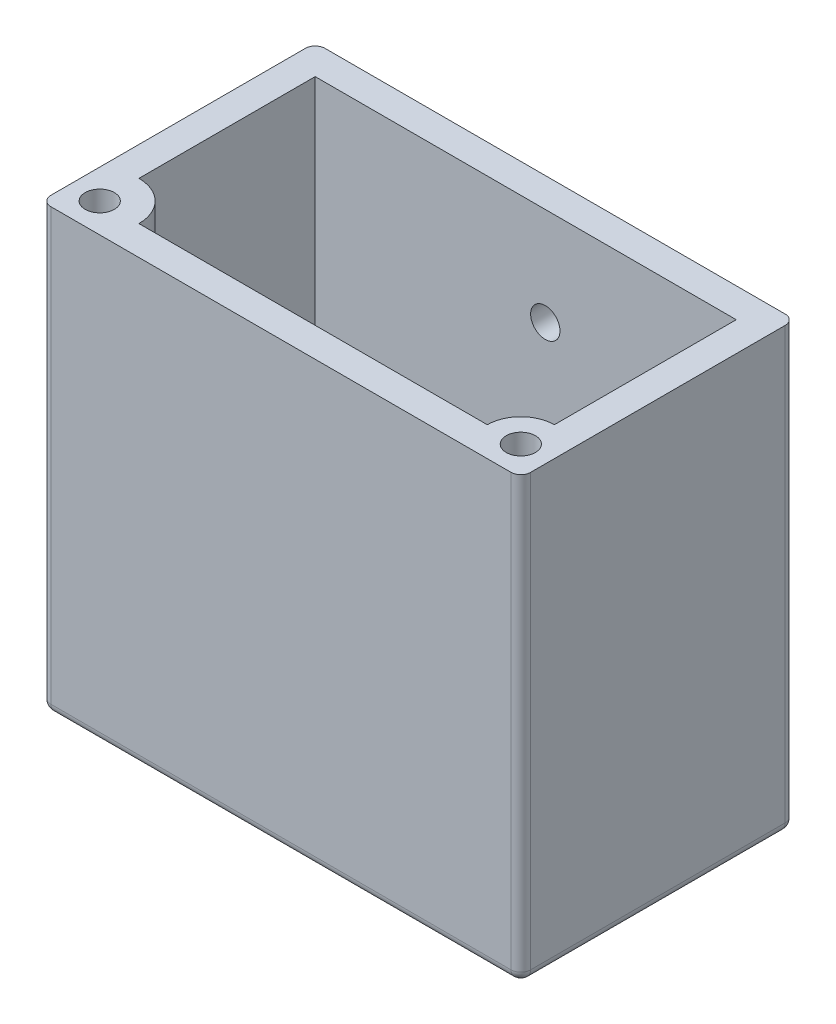
SolidWorks part; units mm, degrees
ref_plane "Front Plane" through (0, 0, 0) normal (0, 0, 1) x (1, 0, 0)
ref_plane "Top Plane" through (0, 0, 0) normal (0, 1, 0) x (1, 0, 0)
ref_plane "Right Plane" through (0, 0, 0) normal (1, 0, 0) x (0, 0, -1)
sketch "Sketch1" plane through (0, 0, 0) normal (0, 1, 0) x (1, 0, 0)
  line L1 (-29.4867, 17.2212) -> (19.5133, 17.2212)
  line L2 (-29.4867, 17.2212) -> (-29.4867, -10.7788)
  line L3 (-29.4867, -10.7788) -> (19.5133, -10.7788)
  line L4 (19.5133, 17.2212) -> (19.5133, -10.7788)
  dimension "D1" = 28
  dimension "D2" = 49
extrude "Boss-Extrude1" add sketch "Sketch1" along normal blind 45
sketch "Sketch2" plane through (0, 45, 0) normal (0, 1, 0) x (1, 0, 0)
  line L0 (-29.4867, -10.7788) -> (19.5133, -10.7788) construction
  line L1 (16.5133, -7.7788) -> (-26.4867, -7.7788)
  line L2 (16.5133, -7.7788) -> (16.5133, 14.2212)
  line L3 (16.5133, 14.2212) -> (-26.4867, 14.2212)
  line L4 (-26.4867, -7.7788) -> (-26.4867, 14.2212)
  line L5 (-29.4867, 17.2212) -> (-29.4867, -10.7788) construction
  line L6 (19.5133, 17.2212) -> (-29.4867, 17.2212) construction
  line L7 (19.5133, -10.7788) -> (19.5133, 17.2212) construction
  dimension "D1" = 3
  dimension "D2" = 3
  dimension "D3" = 3
  dimension "D4" = 3
extrude "Cut-Extrude1" cut sketch "Sketch2" against normal blind 43
sketch "Sketch3" plane through (0, 2, 0) normal (0, 1, 0) x (1, 0, 0)
  line L0 (16.5133, 14.2212) -> (-26.4867, 14.2212) construction
  line L1 (9.5133, 3.2212) -> (-19.4867, 3.2212)
  line L2 (9.5133, 3.2212) -> (9.5133, 11.2212)
  line L3 (9.5133, 11.2212) -> (-19.4867, 11.2212)
  line L4 (-19.4867, 3.2212) -> (-19.4867, 11.2212)
  line L5 (16.5133, -7.7788) -> (16.5133, 14.2212) construction
  line L6 (-26.4867, 14.2212) -> (-26.4867, -7.7788) construction
  dimension "D1" = 8
  dimension "D2" = 3
  dimension "D3" = 7
  dimension "D4" = 7
extrude "Cut-Extrude2" cut sketch "Sketch3" against normal blind 3
sketch "Sketch4" plane through (0, 0, -14.2212) normal (0, 0, 1) x (1, 0, 0)
  line L0 (16.5133, 2) -> (-26.4867, 2) construction
  line L1 (16.5133, 2) -> (16.5133, 45) construction
  circle A0 centre (-2.9867, 35) radius 1.5
  dimension "D1" = 33
  dimension "D2" = 19.5
extrude "Cut-Extrude3" cut sketch "Sketch4" against normal blind 3
sketch "Sketch5" plane through (0, 0, 0) normal (0, -1, 0) x (1, 0, 0)
  line L0 (19.5133, 10.7788) -> (19.5133, -17.2212) construction
  line L1 (-29.4867, 10.7788) -> (19.5133, 10.7788) construction
  line L2 (14.8675, 10.7788) -> (19.5133, 10.7788)
  line L3 (19.5133, 10.7788) -> (19.5133, 6.133)
  arc A0 (14.8675, 10.7788) -> (19.5133, 6.133) centre (16.5133, 7.7788) ccw
  dimension "D1" = 3
  dimension "D2" = 3
extrude "Boss-Extrude2" add sketch "Sketch5" against normal blind 45
sketch "Sketch6" plane through (0, 0, 0) normal (0, -1, 0) x (1, 0, 0)
  line L0 (19.5133, 10.7788) -> (19.5133, -17.2212) construction
  line L1 (-29.4867, 10.7788) -> (19.5133, 10.7788) construction
  circle A0 centre (16.5133, 7.7788) radius 1.49
  dimension "D1" = 3
  dimension "D2" = 3
extrude "Cut-Extrude4" cut sketch "Sketch6" against normal blind 45
sketch "Sketch7" plane through (0, 0, 0) normal (0, -1, 0) x (1, 0, 0)
  line L0 (-29.4867, 10.7788) -> (19.5133, 10.7788) construction
  line L1 (-29.4867, -17.2212) -> (-29.4867, 10.7788) construction
  line L2 (-29.4867, 5.133) -> (-29.4867, 10.7788)
  line L3 (-29.4867, 10.7788) -> (-23.841, 10.7788)
  arc A0 (-29.4867, 5.133) -> (-23.841, 10.7788) centre (-26.4867, 7.7788) ccw
  dimension "D1" = 3
  dimension "D2" = 3
extrude "Boss-Extrude3" add sketch "Sketch7" against normal blind 45
sketch "Sketch8" plane through (0, 0, 0) normal (0, -1, 0) x (1, 0, 0)
  line L0 (-29.4867, -17.2212) -> (-29.4867, 10.7788) construction
  line L1 (-29.4867, 10.7788) -> (19.5133, 10.7788) construction
  circle A0 centre (-26.4867, 7.7788) radius 1.49
  dimension "D1" = 3
  dimension "D2" = 3
extrude "Cut-Extrude5" cut sketch "Sketch8" against normal blind 45
fillet "Fillet2" radius 1 8 edges at (19.5133, 0, -3.2212) (19.5133, 22.5, -17.2212) (-4.9867, 0, -17.2212) (-29.4867, 22.5, -17.2212) (-29.4867, 0, -3.2212) (19.5133, 22.5, 10.7788) (-29.4867, 22.5, 10.7788) (-4.9867, 0, 10.7788)
